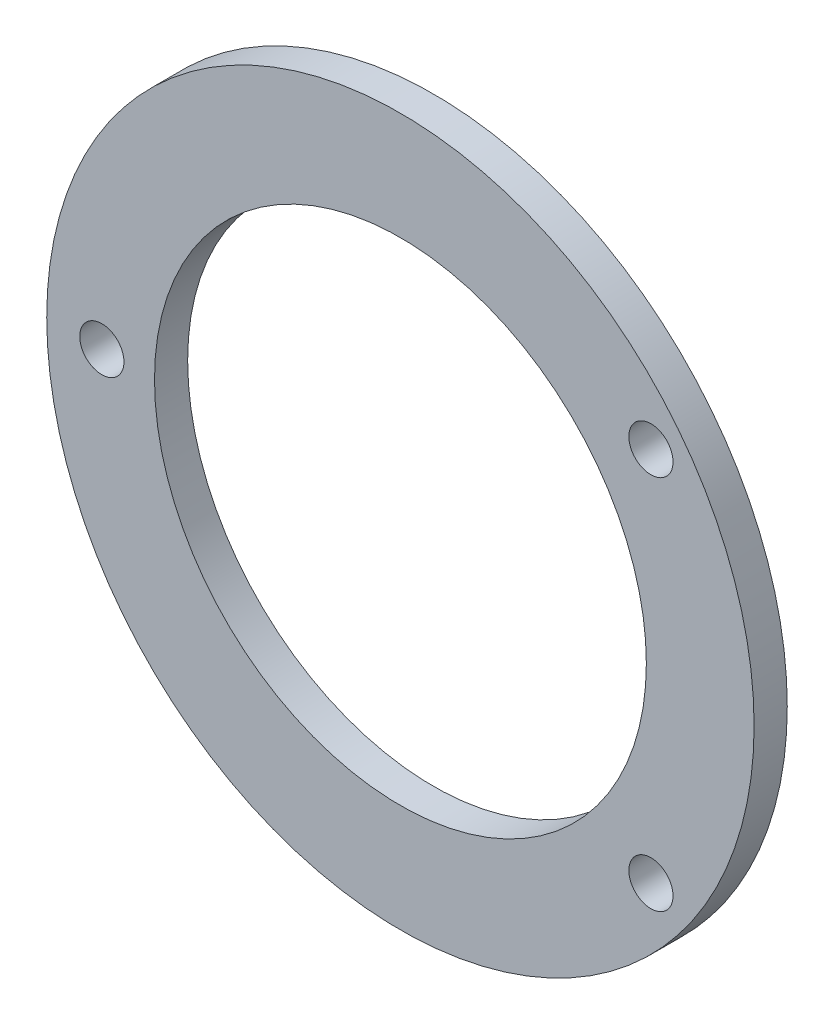
SolidWorks part; units mm, degrees
ref_plane "Front Plane" through (0, 0, 0) normal (0, 0, 1) x (1, 0, 0)
ref_plane "Top Plane" through (0, 0, 0) normal (0, 1, 0) x (1, 0, 0)
ref_plane "Right Plane" through (0, 0, 0) normal (1, 0, 0) x (0, 0, -1)
sketch "Sketch1" plane through (0, 0, 0) normal (0, 0, 1) x (1, 0, 0)
  line L0 (-2.3105, 2.6217) -> (-21.9327, 22.2439) construction
  line L1 (-2.3105, 2.6217) -> (-21.9327, -17.0005) construction
  line L2 (-2.3105, 2.6217) -> (25.4395, 2.6217) construction
  line L3 (-21.9327, 22.2439) -> (-21.9327, -17.0005) construction
  line L4 (-41.555, 41.8661) -> (-41.555, -36.6227) construction
  line L5 (-56.3481, 2.6217) -> (51.727, 2.6217) construction
  line L6 (-2.3105, 38.7539) -> (-2.3105, -33.5105) construction
  line L7 (-2.3105, 2.6217) -> (53.1895, 2.6217) construction
  line L8 (-2.3105, 74.886) -> (-2.3105, -69.6426) construction
  line L9 (-110.3856, 2.6217) -> (105.7646, 2.6217) construction
  line L10 (-2.3105, 2.6217) -> (-41.555, -36.6227) construction
  line L11 (-2.3105, 2.6217) -> (-41.555, 41.8661) construction
  circle A8 centre (-2.3105, 2.6217) radius 44.5
  circle A11 centre (-2.3105, 2.6217) radius 64
  circle A13 centre (43.0195, -31.3783) radius 4
  circle A14 centre (43.0195, 36.6217) radius 4
  circle A15 centre (-56.3405, 2.6217) radius 4
  point P2 (-2.3105, 2.6217)
  point P16 (-2.3105, 2.6217)
  point P20 (-2.3105, 2.6217)
  point P33 (-2.3105, 2.6217)
  dimension "D1" = 128
  dimension "D2" = 89
  dimension "D5" = 34
  dimension "D3" = 27.75
  dimension "D4" = 90
  dimension "D6" = 34
  dimension "D7" = 99.36
  dimension "D8" = 99.36
  dimension "D9" = 54.03
extrude "Boss-Extrude1" add sketch "Sketch1" along normal blind 6
